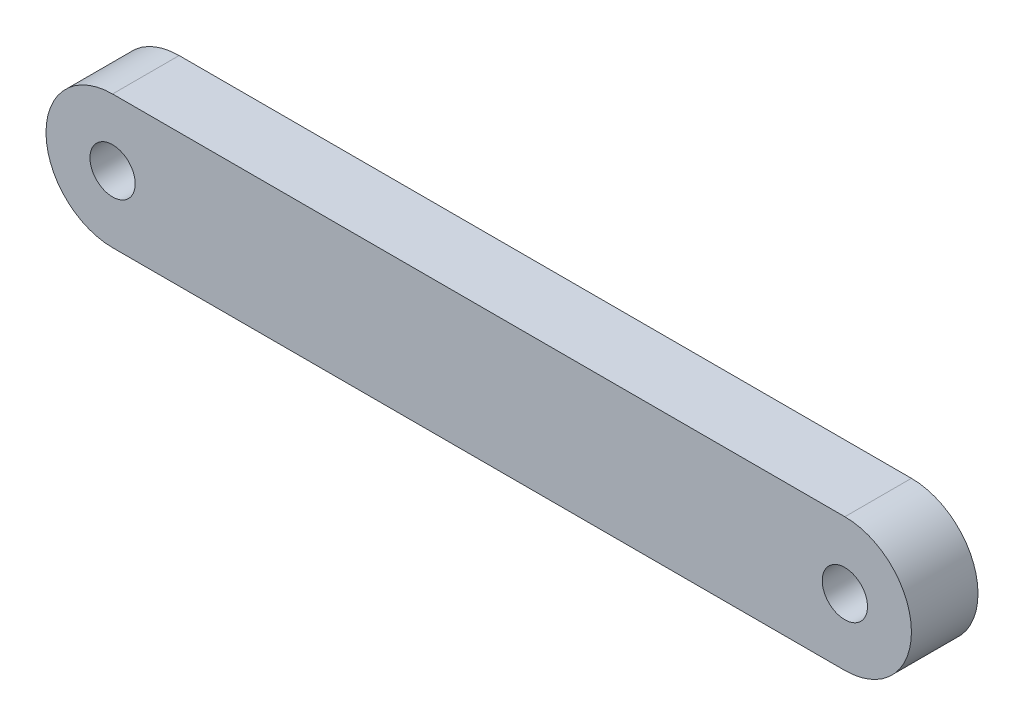
SolidWorks part; units mm, degrees
material "1060 Alloy"
ref_plane "Front" through (0, 0, 0) normal (0, 0, 1) x (1, 0, 0)
ref_plane "Top" through (0, 0, 0) normal (0, 1, 0) x (1, 0, 0)
ref_plane "Right" through (0, 0, 0) normal (1, 0, 0) x (0, 0, -1)
sketch "Sketch1" plane through (0, 0, 0) normal (0, 0, 1) x (1, 0, 0)
  line L0 (0, 0) -> (69.85, 0) construction
  line L2 (0, 6.35) -> (69.85, 6.35)
  line L3 (0, -6.35) -> (69.85, -6.35)
  arc A0 (0, 6.35) -> (0, -6.35) centre (0, 0) ccw
  arc A1 (69.85, -6.35) -> (69.85, 6.35) centre (69.85, 0) ccw
  circle A2 centre (0, 0) radius 2.159
  circle A3 centre (69.85, 0) radius 2.159
  point P5 (34.925, 0)
  dimension "D1" = 4.318
  dimension "D2" = 69.85
  dimension "D3" = 6.35
extrude "Boss-Extrude1" add sketch "Sketch1" along normal blind 6.35
